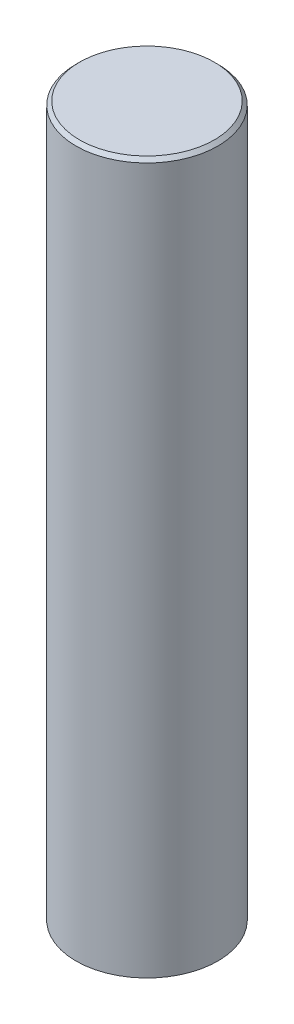
SolidWorks part; units mm, degrees
ref_plane "Front Plane" through (0, 0, 0) normal (0, 0, 1) x (1, 0, 0)
ref_plane "Top Plane" through (0, 0, 0) normal (0, 1, 0) x (1, 0, 0)
ref_plane "Right Plane" through (0, 0, 0) normal (1, 0, 0) x (0, 0, -1)
sketch "Sketch1" plane through (0, 0, 0) normal (0, 1, 0) x (1, 0, 0)
  circle A0 centre (0, 0) radius 20
  dimension "D1" = 40
extrude "Boss-Extrude1" add sketch "Sketch1" along normal blind 200
chamfer "Chamfer1" distance 1 angle 45 1 edges at (0, 200, 20)
